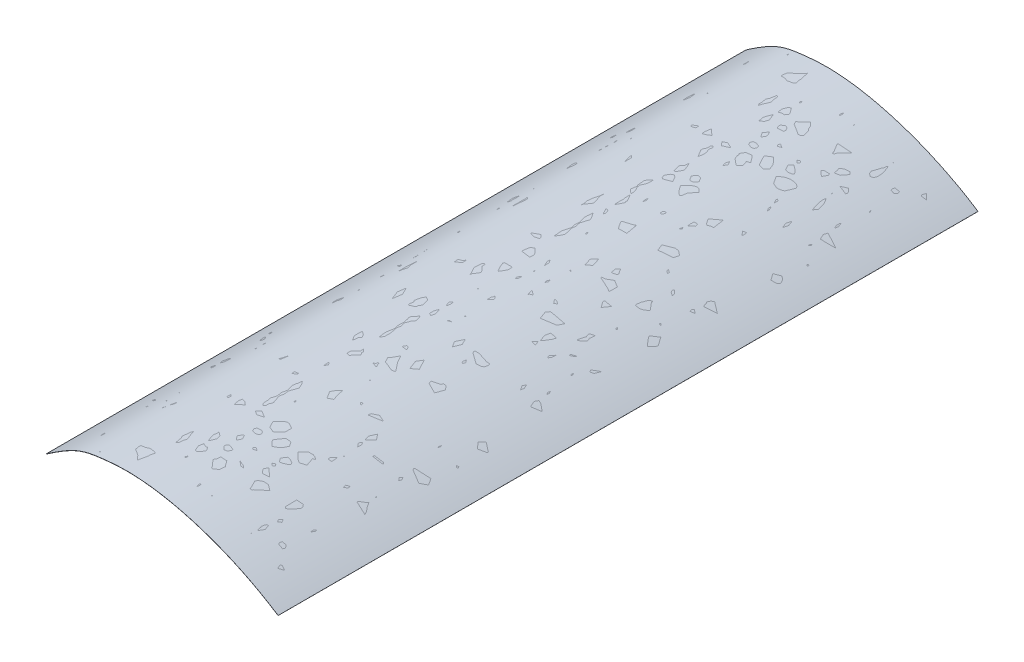
SolidWorks part; units mm, degrees
ref_plane "Front Plane" through (0, 0, 0) normal (0, 0, 1) x (1, 0, 0)
ref_plane "Top Plane" through (0, 0, 0) normal (0, 1, 0) x (1, 0, 0)
ref_plane "Right Plane" through (0, 0, 0) normal (1, 0, 0) x (0, 0, -1)
sketch "Sketch1" plane through (0, 0, 0) normal (0, 0, 1) x (1, 0, 0)
  line L0 (-169.0031, 11.7142) -> (-694.187, 895.1707) construction
  line L1 (-1743.6649, 593.9127) -> (-1743.608, 593.8305)
  line L2 (-1544.595, 573.525) -> (-1544.65, 573.4414)
  spline S0 degree 3 poles (-1743.608, 593.8305) (-1719.5079, 610.5378) (-1709.3895, 613.3998) (-1646.2803, 619.2418) (-1585.7166, 600.4239) (-1544.65, 573.4414) knots 0 0 0 0 0.320555 0.420555 1 1 1 1
  spline S1 degree 1 poles (-1743.6649, 593.9127) (-1544.595, 573.525) knots 0 0 1 1 construction
  spline S2 degree 3 poles (-1743.6649, 593.9127) (-1743.0879, 594.3127) (-1741.9172, 595.1205) (-1739.6885, 596.6426) (-1737.0242, 598.431) (-1734.0301, 600.3862) (-1730.275, 602.7582) (-1725.9851, 605.3047) (-1721.3377, 607.7711) (-1717.0471, 609.7272) (-1711.6104, 611.7601) (-1704.9855, 613.4224) (-1697.649, 614.4326) (-1690.7443, 615.1888) (-1683.1917, 615.8568) (-1672.8523, 616.2509) (-1659.6402, 615.5242) (-1645.7441, 613.7084) (-1631.355, 610.828) (-1616.6452, 606.9304) (-1601.7921, 602.0566) (-1586.9719, 596.2497) (-1572.3602, 589.5513) (-1560.5078, 583.2639) (-1551.3008, 577.8269) (-1546.8169, 574.9849) (-1544.595, 573.525) knots 0 0 0 0 0.007812 0.015625 0.03125 0.046875 0.0625 0.09375 0.125 0.15625 0.1875 0.25 0.3125 0.34375 0.375 0.4375 0.5 0.5625 0.625 0.6875 0.75 0.8125 0.875 0.9375 0.96875 1 1 1 1
  dimension "D1" = 0.1
extrude "Boss-Extrude1" add sketch "Sketch1" along normal blind 600.2
